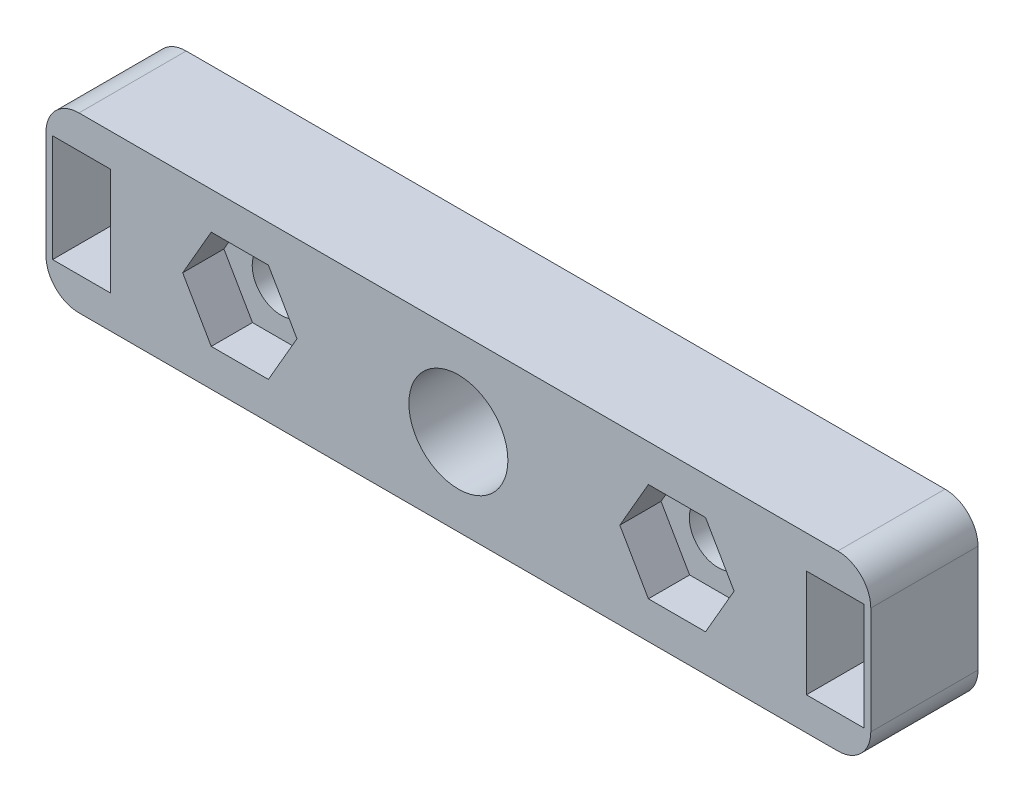
SolidWorks part; units mm, degrees
ref_plane "正面" through (0, 0, 0) normal (0, 0, 1) x (1, 0, 0)
ref_plane "平面" through (0, 0, 0) normal (0, 1, 0) x (1, 0, 0)
ref_plane "右側面" through (0, 0, 0) normal (1, 0, 0) x (0, 0, -1)
sketch "ｽｹｯﾁ1" plane through (0, 0, 0) normal (0, 0, 1) x (1, 0, 0)
  line L5 (0, 0) -> (50, 0)
  line L6 (0, 0) -> (0, 10.5)
  line L7 (0, 10.5) -> (50, 10.5)
  line L8 (50, 0) -> (50, 10.5)
  dimension "D1" = 10.5
  dimension "D2" = 50
extrude "ﾎﾞｽ - 押し出し1" add sketch "ｽｹｯﾁ1" along normal blind 17
sketch "ｽｹｯﾁ2" plane through (0, 0, 17) normal (0, 0, 1) x (1, 0, 0)
  line L0 (0, 5.25) -> (50, 5.25) construction
  line L1 (0, 10.5) -> (0, 0) construction
  line L2 (50, 0) -> (50, 10.5) construction
  line L3 (25, 10.5) -> (25, 0) construction
  line L4 (50, 10.5) -> (0, 10.5) construction
  line L5 (0, 0) -> (50, 0) construction
  line L11 (7, 3.5) -> (43, 3.5)
  line L12 (7, 3.5) -> (7, 7)
  line L13 (7, 7) -> (43, 7)
  line L14 (43, 3.5) -> (43, 7)
  line L15 (7, 3.5) -> (43, 7) construction
  line L16 (7, 7) -> (43, 3.5) construction
  point P12 (25, 5.25)
  point P17 (25, 5.25)
  dimension "D1" = 3.5
  dimension "D2" = 36
extrude "ｶｯﾄ - 押し出し1" cut sketch "ｽｹｯﾁ2" against normal blind 10
sketch "ｽｹｯﾁ3" plane through (0, 0, 0) normal (0, -1, 0) x (1, 0, 0)
  line L0 (1, 17) -> (3, 12)
  line L1 (0, 17) -> (50, 17) construction
  line L2 (3, 12) -> (7, 12)
  line L3 (7, 12) -> (17, 17)
  line L4 (17, 17) -> (1, 17)
  line L5 (33, 17) -> (43, 12)
  line L6 (43, 12) -> (47, 12)
  line L7 (47, 12) -> (49, 17)
  line L8 (49, 17) -> (33, 17)
  line L9 (0, 17) -> (0, 0) construction
  line L10 (50, 17) -> (50, 0) construction
  dimension "D1" = 1
  dimension "D2" = 1
  dimension "D3" = 3
  dimension "D4" = 3
  dimension "D5" = 17
  dimension "D6" = 17
  dimension "D7" = 5
  dimension "D8" = 5
  dimension "D9" = 7
  dimension "D10" = 7
extrude "ｶｯﾄ - 押し出し2" cut sketch "ｽｹｯﾁ3" against normal up to surface (10.5 mm away) up to face at (25, 10.5, 8.5)
sketch "ｽｹｯﾁ4" plane through (0, 0, 0) normal (0, 0, -1) x (-1, 0, 0)
  line L0 (-25, 0) -> (-25, 10.5) construction
  line L1 (0, 0) -> (-50, 0) construction
  line L2 (-50, 10.5) -> (0, 10.5) construction
  line L3 (0, 5.25) -> (-50, 5.25) construction
  line L4 (0, 10.5) -> (0, 0) construction
  line L5 (-50, 0) -> (-50, 10.5) construction
  line L6 (-0.4, 5.25) -> (-3.9, 5.25) construction
  line L7 (-0.4, 8.5) -> (-3.9, 8.5)
  line L8 (-0.4, 8.5) -> (-0.4, 2)
  line L9 (-0.4, 2) -> (-3.9, 2)
  line L10 (-3.9, 8.5) -> (-3.9, 2)
  line L11 (-2.15, 2) -> (-2.15, 8.5) construction
  line L12 (-49.6, 8.5) -> (-49.6, 2)
  line L13 (-49.6, 2) -> (-46.1, 2)
  line L14 (-46.1, 8.5) -> (-46.1, 2)
  line L15 (-49.6, 8.5) -> (-46.1, 8.5)
  dimension "D1" = 3.5
  dimension "D2" = 6.5
  dimension "D3" = 0.4
extrude "ｶｯﾄ - 押し出し3" cut sketch "ｽｹｯﾁ4" against normal blind 6.5
fillet "ﾌｨﾚｯﾄ1" radius 2 4 edges at (0, 0, 8.5) (0, 10.5, 8.5) (50, 0, 8.5) (50, 10.5, 8.5)
ref_plane "この面でカットした部品を印刷" through (0, 0, 6.5) normal (0, 0, -1) x (-1, 0, 0)
sketch "ｽｹｯﾁ6" plane through (0, 0, 0) normal (0, 0, -1) x (-1, 0, 0)
  line L0 (-50, 5.25) -> (0, 5.25) construction
  line L1 (-50, 2) -> (-50, 8.5) construction
  line L2 (0, 8.5) -> (0, 2) construction
  line L3 (-25, 10.5) -> (-25, 0) construction
  line L4 (-48, 10.5) -> (-2, 10.5) construction
  line L5 (-2, 0) -> (-48, 0) construction
  circle A0 centre (-25, 5.25) radius 3
  circle A1 centre (-11.75, 5.25) radius 1.75
  circle A2 centre (-38.25, 5.25) radius 1.75
  dimension "D1" = 6
  dimension "D2" = 3.5
  dimension "D3" = 3.5
  dimension "D4" = 13.25
  dimension "D5" = 13.25
extrude "ｶｯﾄ - 押し出し4" cut sketch "ｽｹｯﾁ6" against normal through all
sketch "ｽｹｯﾁ7" plane through (0, 0, 7) normal (0, 0, 1) x (1, 0, 0)
  line L0 (38.25, 7) -> (27.4367, 7) construction
  line L1 (34.7859, 5.25) -> (36.5179, 2.25)
  line L2 (36.5179, 2.25) -> (39.9821, 2.25)
  line L3 (39.9821, 2.25) -> (41.7141, 5.25)
  line L4 (41.7141, 5.25) -> (39.9821, 8.25)
  line L5 (39.9821, 8.25) -> (36.5179, 8.25)
  line L6 (36.5179, 8.25) -> (34.7859, 5.25)
  line L7 (43, 5.25) -> (7, 5.25) construction
  line L9 (43, 3.5) -> (43, 7) construction
  line L10 (7, 7) -> (7, 3.5) construction
  line L11 (25, 5.25) -> (25, 0.6326) construction
  line L12 (25, 5.25) -> (25, 9.2813) construction
  line L13 (13.4821, 8.25) -> (15.2141, 5.25)
  line L14 (10.0179, 8.25) -> (13.4821, 8.25)
  line L15 (8.2859, 5.25) -> (10.0179, 8.25)
  line L16 (10.0179, 2.25) -> (8.2859, 5.25)
  line L17 (13.4821, 2.25) -> (10.0179, 2.25)
  line L18 (15.2141, 5.25) -> (13.4821, 2.25)
  circle A0 centre (38.25, 5.25) radius 3 construction
  circle A1 centre (11.75, 5.25) radius 3 construction
  dimension "D1" = 6
  dimension "D2" = 120
extrude "ｶｯﾄ - 押し出し5" cut sketch "ｽｹｯﾁ7" along normal through all
sketch "ｽｹｯﾁ8" plane through (0, 0, 7) normal (0, 0, 1) x (1, 0, 0)
  line L0 (43, 5.25) -> (7, 5.25) construction
  line L1 (36.5179, 2.25) -> (39.9821, 2.25)
  line L2 (39.9821, 2.25) -> (41.7141, 5.25)
  line L3 (41.7141, 5.25) -> (39.9821, 8.25)
  line L4 (39.9821, 8.25) -> (36.5179, 8.25)
  line L5 (36.5179, 8.25) -> (34.7859, 5.25)
  line L6 (34.7859, 5.25) -> (36.5179, 2.25)
  line L7 (43, 3.5) -> (43, 7) construction
  line L8 (7, 7) -> (7, 3.5) construction
  line L9 (25, 5.25) -> (25, 3.6623) construction
  line L10 (15.2141, 5.25) -> (13.4821, 2.25)
  line L11 (13.4821, 8.25) -> (15.2141, 5.25)
  line L12 (10.0179, 8.25) -> (13.4821, 8.25)
  line L13 (8.2859, 5.25) -> (10.0179, 8.25)
  line L14 (10.0179, 2.25) -> (8.2859, 5.25)
  line L15 (13.4821, 2.25) -> (10.0179, 2.25)
  circle A0 centre (38.25, 5.25) radius 3 construction
  circle A1 centre (11.75, 5.25) radius 3 construction
extrude "ｶｯﾄ - 押し出し6" cut sketch "ｽｹｯﾁ8" against normal blind 3
sketch "ｽｹｯﾁ9" plane through (0, 0, 6.5) normal (0, 0, -1) x (-1, 0, 0)
  line L5 (-54.1814, -6.3116) -> (4.2397, -6.3116)
  line L6 (-54.1814, -6.3116) -> (-54.1814, 17.9335)
  line L7 (-54.1814, 17.9335) -> (4.2397, 17.9335)
  line L8 (4.2397, -6.3116) -> (4.2397, 17.9335)
extrude "ｶｯﾄ - 押し出し7" cut sketch "ｽｹｯﾁ9" against normal through all
